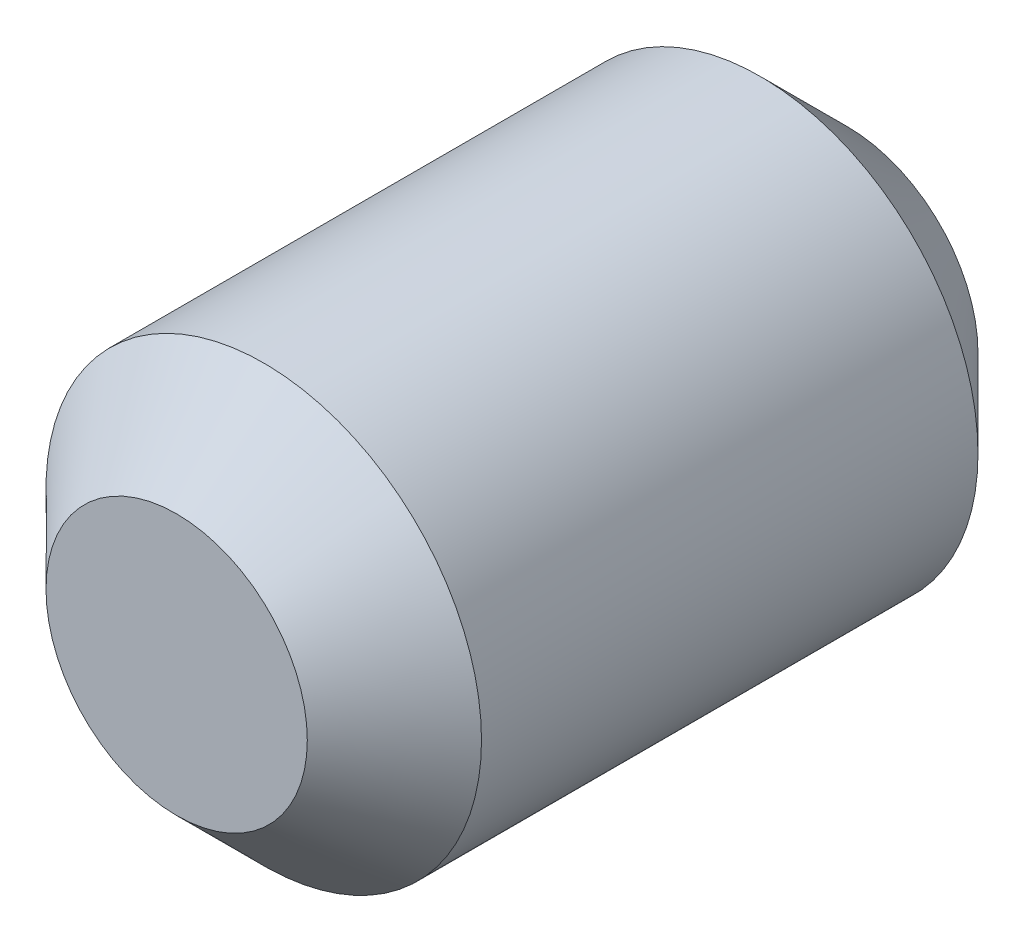
SolidWorks part; units mm, degrees
ref_plane "Face" through (0, 0, 0) normal (0, 0, 1) x (1, 0, 0)
ref_plane "Dessus" through (0, 0, 0) normal (0, 1, 0) x (1, 0, 0)
ref_plane "Droite" through (0, 0, 0) normal (1, 0, 0) x (0, 0, -1)
sketch "Esquisse1" plane through (0, 0, 0) normal (0, 0, 1) x (1, 0, 0)
  circle A0 centre (0, 0) radius 2.5
  dimension "D1" = 5
extrude "Base-Extrusion" add sketch "Esquisse1" along normal mid plane 7.7
chamfer "Chanfrein1" distance 1 angle 45
